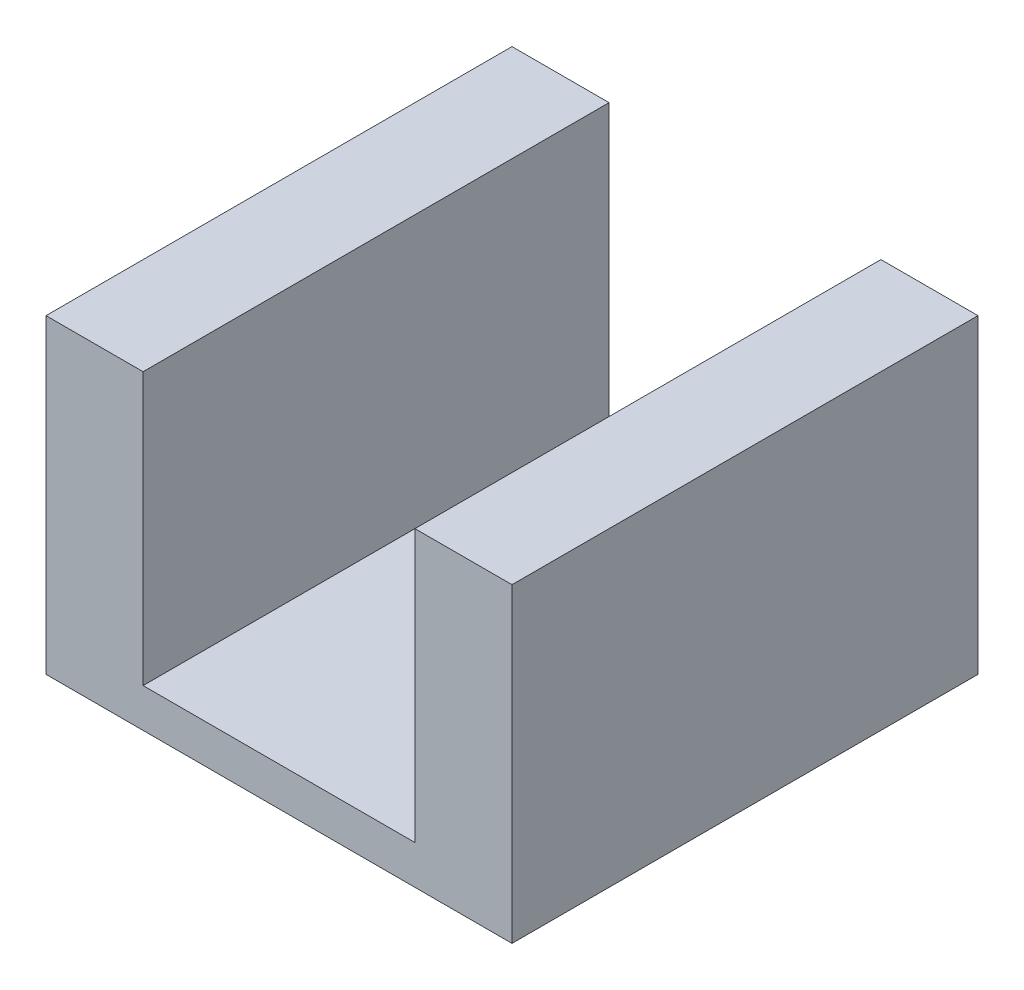
SolidWorks part; units mm, degrees
material "6063-O"
ref_plane "Front" through (0, 0, 0) normal (0, 0, 1) x (1, 0, 0)
ref_plane "Top" through (0, 0, 0) normal (0, 1, 0) x (1, 0, 0)
ref_plane "Right" through (0, 0, 0) normal (1, 0, 0) x (0, 0, -1)
sketch "Sketch1" plane through (0, 0, 0) normal (0, 0, 1) x (1, 0, 0)
  line L0 (0, 0) -> (0, 61400.5293) construction
  line L1 (22.225, 0) -> (-22.225, 0)
  line L2 (-22.225, 0) -> (-22.225, 44.45)
  line L3 (-22.225, 44.45) -> (-38.1, 44.45)
  line L4 (-38.1, 44.45) -> (-38.1, -6.35)
  line L5 (-38.1, -6.35) -> (38.1, -6.35)
  line L6 (38.1, 44.45) -> (38.1, -6.35)
  line L7 (22.225, 0) -> (22.225, 44.45)
  line L8 (22.225, 44.45) -> (38.1, 44.45)
  point P13 (0, 0)
  point P14 (0, -6.35)
  dimension "D1" = 15.875
  dimension "D2" = 50.8
  dimension "D3" = 6.35
  dimension "D4" = 38.1
extrude "Boss-Extrude1" add sketch "Sketch1" along normal blind 76.2
sketch "Sketch2" plane through (0, 0, 0) normal (0, 1, 0) x (1, 0, 0)
  line L0 (0, 0) -> (0, -76.2) construction
  line L1 (22.225, -76.2) -> (-22.225, -76.2) construction
  circle A0 centre (0, -38.1) radius 7.9375
  dimension "D1" = 15.875
extrude "Cut-Extrude1" cut sketch "Sketch2" against normal through all
